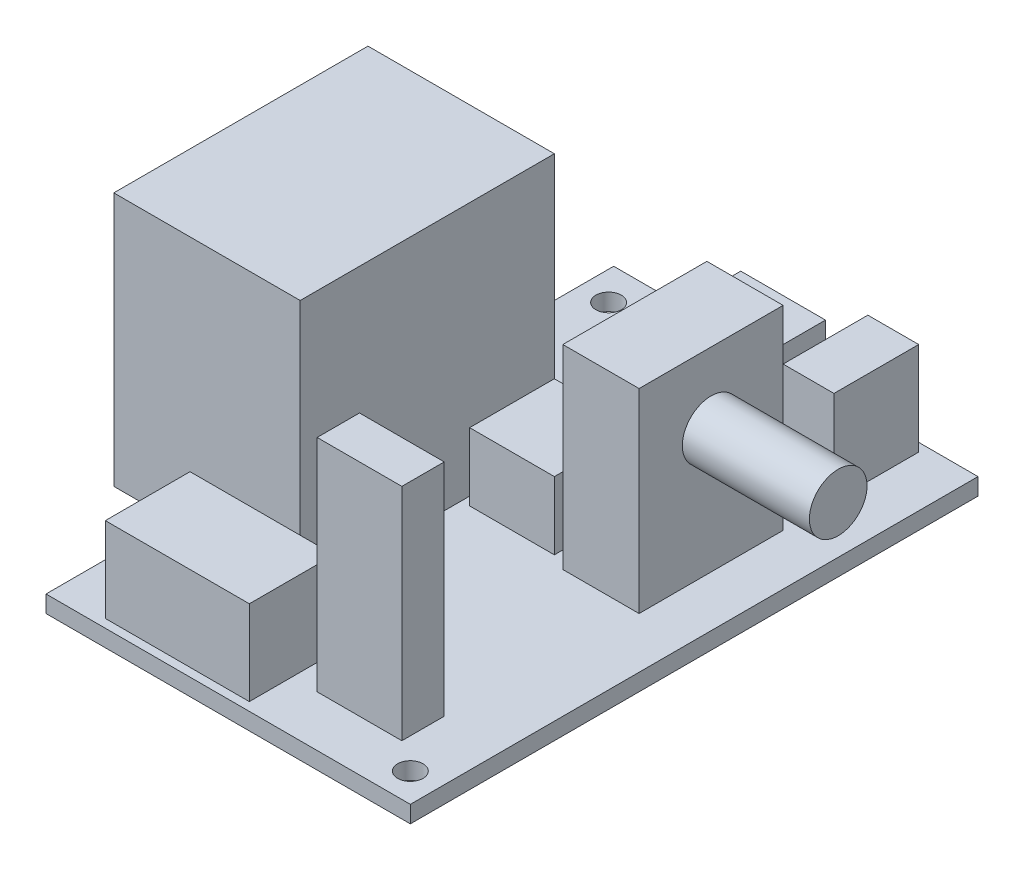
SolidWorks part; units mm, degrees
ref_plane "Front Plane" through (0, 0, 0) normal (0, 0, 1) x (1, 0, 0)
ref_plane "Top Plane" through (0, 0, 0) normal (0, 1, 0) x (1, 0, 0)
ref_plane "Right Plane" through (0, 0, 0) normal (1, 0, 0) x (0, 0, -1)
sketch "Sketch1" plane through (0, 0, 0) normal (0, 1, 0) x (1, 0, 0)
  line L1 (-21.5, -56) -> (21.5, -56)
  line L2 (-21.5, -56) -> (-21.5, 56)
  line L3 (-21.5, 56) -> (21.5, 56)
  line L4 (21.5, -56) -> (21.5, 56)
  line L5 (-21.5, -56) -> (21.5, 56) construction
  line L6 (-21.5, 56) -> (21.5, -56) construction
  circle A0 centre (18.1, -52.6) radius 1.5
  circle A1 centre (-16.5, 52) radius 1.5
  circle A2 centre (-18.1, 7) radius 1.5
  point P0 (0, 0)
  point P12 (0, 0)
  point P14 (-17.8353, -15.6172)
  dimension "D3" = 3
  dimension "D6" = 3
  dimension "D7" = 5
  dimension "D9" = 3
  dimension "D1" = 112
  dimension "D2" = 43
  dimension "D4" = 3.4
  dimension "D5" = 3.4
  dimension "D8" = 4
  dimension "D10" = 3.4
  dimension "D11" = 63
extrude "Board" add sketch "Sketch1" along normal blind 2
sketch "Sketch2" plane through (0, 2, 0) normal (0, 1, 0) x (1, 0, 0)
  line L0 (21.5, 56) -> (-21.5, 56) construction
  line L1 (16.5, 51) -> (0.5, 51)
  line L2 (16.5, 51) -> (16.5, 11)
  line L3 (16.5, 11) -> (0.5, 11)
  line L4 (0.5, 51) -> (0.5, 11)
  line L5 (16.5, 51) -> (0.5, 11) construction
  line L6 (16.5, 11) -> (0.5, 51) construction
  line L7 (21.5, -56) -> (21.5, 56) construction
  line L9 (9.5, 10) -> (15.5, 10)
  line L10 (9.5, 10) -> (9.5, 0)
  line L11 (9.5, 0) -> (15.5, 0)
  line L12 (15.5, 10) -> (15.5, 0)
  line L13 (9.5, 10) -> (15.5, 0) construction
  line L14 (9.5, 0) -> (15.5, 10) construction
  point P4 (8.5, 31)
  point P13 (12.5, 5)
  dimension "D1" = 40
  dimension "D2" = 16
  dimension "D3" = 5
  dimension "D4" = 5
  dimension "D5" = 10
  dimension "D6" = 6
  dimension "D7" = 6
  dimension "D8" = 46
extrude "7SEG" add sketch "Sketch2" along normal blind 11
sketch "Sketch3" plane through (0, 2, 0) normal (0, 1, 0) x (1, 0, 0)
  line L0 (21.5, 56) -> (-21.5, 56) construction
  line L1 (-11.5, 36) -> (-1.5, 36)
  line L2 (-11.5, 36) -> (-11.5, 16)
  line L3 (-11.5, 16) -> (-1.5, 16)
  line L4 (-1.5, 36) -> (-1.5, 16)
  line L5 (-11.5, 36) -> (-1.5, 16) construction
  line L6 (-11.5, 16) -> (-1.5, 36) construction
  line L7 (-21.5, 56) -> (-21.5, -56) construction
  line L9 (-5.5, 10) -> (4.5, 10)
  line L10 (-5.5, 10) -> (-5.5, 0)
  line L11 (-5.5, 0) -> (4.5, 0)
  line L12 (4.5, 10) -> (4.5, 0)
  line L13 (-5.5, 10) -> (4.5, 0) construction
  line L14 (-5.5, 0) -> (4.5, 10) construction
  line L15 (-5.5, -12) -> (4.5, -12)
  line L16 (-5.5, -12) -> (-5.5, -22)
  line L17 (-5.5, -22) -> (4.5, -22)
  line L18 (4.5, -12) -> (4.5, -22)
  line L19 (-5.5, -12) -> (4.5, -22) construction
  line L20 (-5.5, -22) -> (4.5, -12) construction
  point P4 (-6.5, 26)
  point P13 (-0.5, 5)
  point P18 (-0.5, -17)
  point P19 (-5.5, -17)
  dimension "D1" = 20
  dimension "D2" = 10
  dimension "D3" = 20
  dimension "D4" = 10
  dimension "D5" = 10
  dimension "D6" = 46
  dimension "D7" = 16
  dimension "D8" = 10
  dimension "D9" = 16
  dimension "D10" = 68
extrude "IC" add sketch "Sketch3" along normal blind 8
sketch "Sketch5" plane through (0, 2, 0) normal (0, 1, 0) x (1, 0, 0)
  line L0 (21.5, -56) -> (21.5, 56) construction
  line L1 (6.5, -6) -> (15.5, -6)
  line L2 (6.5, -6) -> (6.5, -23)
  line L3 (6.5, -23) -> (15.5, -23)
  line L4 (15.5, -6) -> (15.5, -23)
  line L5 (6.5, -6) -> (15.5, -23) construction
  line L6 (6.5, -23) -> (15.5, -6) construction
  line L7 (9.5, 0) -> (15.5, 0) construction
  point P4 (11, -14.5)
  dimension "D1" = 17
  dimension "D2" = 9
  dimension "D3" = 6
  dimension "D4" = 6
extrude "BienTroA" add sketch "Sketch5" along normal blind 23
sketch "Sketch6" plane through (15.5, 0, 0) normal (1, 0, 0) x (0, 0, -1)
  line L0 (-23, 25) -> (-6, 25) construction
  circle A0 centre (-14.5, 16.6) radius 3.4
  point P9 (-14.5, 25)
  dimension "D1" = 6.8
  dimension "D2" = 8.4
extrude "BienTroB" add sketch "Sketch6" along normal blind 15
sketch "Sketch7" plane through (0, 2, 0) normal (0, 1, 0) x (1, 0, 0)
  line L0 (-21.5, -56) -> (21.5, -56) construction
  line L1 (14.5, -50) -> (4.5, -50)
  line L2 (14.5, -50) -> (14.5, -45)
  line L3 (14.5, -45) -> (4.5, -45)
  line L4 (4.5, -50) -> (4.5, -45)
  line L5 (14.5, -50) -> (4.5, -45) construction
  line L6 (14.5, -45) -> (4.5, -50) construction
  line L7 (21.5, -56) -> (21.5, 56) construction
  point P4 (9.5, -47.5)
  dimension "D1" = 5
  dimension "D2" = 10
  dimension "D3" = 6
  dimension "D4" = 7
extrude "IRF540" add sketch "Sketch7" along normal blind 26
sketch "Sketch8" plane through (0, 2, 0) normal (0, 1, 0) x (1, 0, 0)
  line L0 (-21.5, -56) -> (21.5, -56) construction
  line L1 (-15.5, -45) -> (1.5, -45)
  line L2 (-15.5, -45) -> (-15.5, -55)
  line L3 (-15.5, -55) -> (1.5, -55)
  line L4 (1.5, -45) -> (1.5, -55)
  line L5 (-15.5, -45) -> (1.5, -55) construction
  line L6 (-15.5, -55) -> (1.5, -45) construction
  line L7 (-21.5, 56) -> (-21.5, -56) construction
  point P4 (-7, -50)
  dimension "D1" = 10
  dimension "D2" = 17
  dimension "D3" = 1
  dimension "D4" = 6
extrude "Domino" add sketch "Sketch8" along normal blind 10
sketch "Sketch9" plane through (0, 2, 0) normal (0, 1, 0) x (1, 0, 0)
  line L0 (-21.5, 56) -> (-21.5, -56) construction
  line L1 (-6.5, -41) -> (-28.5, -41)
  line L2 (-6.5, -41) -> (-6.5, -11)
  line L3 (-6.5, -11) -> (-28.5, -11)
  line L4 (-28.5, -41) -> (-28.5, -11)
  line L5 (-6.5, -41) -> (-28.5, -11) construction
  line L6 (-6.5, -11) -> (-28.5, -41) construction
  line L7 (-21.5, -56) -> (21.5, -56) construction
  point P4 (-17.5, -26)
  dimension "D1" = 30
  dimension "D2" = 22
  dimension "D3" = 7
  dimension "D4" = 15
extrude "7805" add sketch "Sketch9" along normal blind 30
sketch "Sketch10" plane through (0, 2, 0) normal (0, 1, 0) x (1, 0, 0)
  line L0 (21.5, 11) -> (-21.5, 11)
  line L1 (21.5, -56) -> (21.5, 56) construction
  line L2 (-21.5, 56) -> (-21.5, -11) construction
split "Split2" trim tools "Sketch10" bodies to split 108 resulting bodies 110 111
delete or keep bodies "Body-Delete/Keep 1" type delete bodies bodies 110
